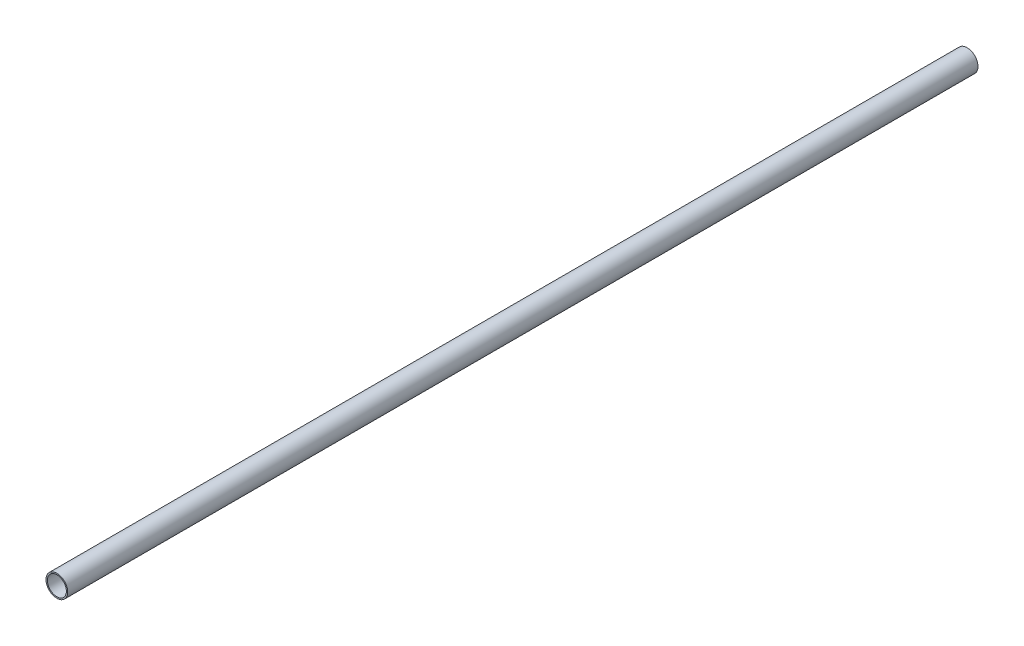
SolidWorks part; units mm, degrees
ref_plane "Plan de face" through (0, 0, 0) normal (0, 0, 1) x (1, 0, 0)
ref_plane "Plan de dessus" through (0, 0, 0) normal (0, 1, 0) x (1, 0, 0)
ref_plane "Plan de droite" through (0, 0, 0) normal (1, 0, 0) x (0, 0, -1)
sketch "Esquisse1" plane through (0, 0, 0) normal (0, 0, 1) x (1, 0, 0)
  circle A0 centre (0, 0) radius 4
  circle A1 centre (0, 0) radius 3.5
  dimension "D1" = 8
  dimension "D2" = 7
extrude "Boss.-Extru.1" add sketch "Esquisse1" along normal blind 335
